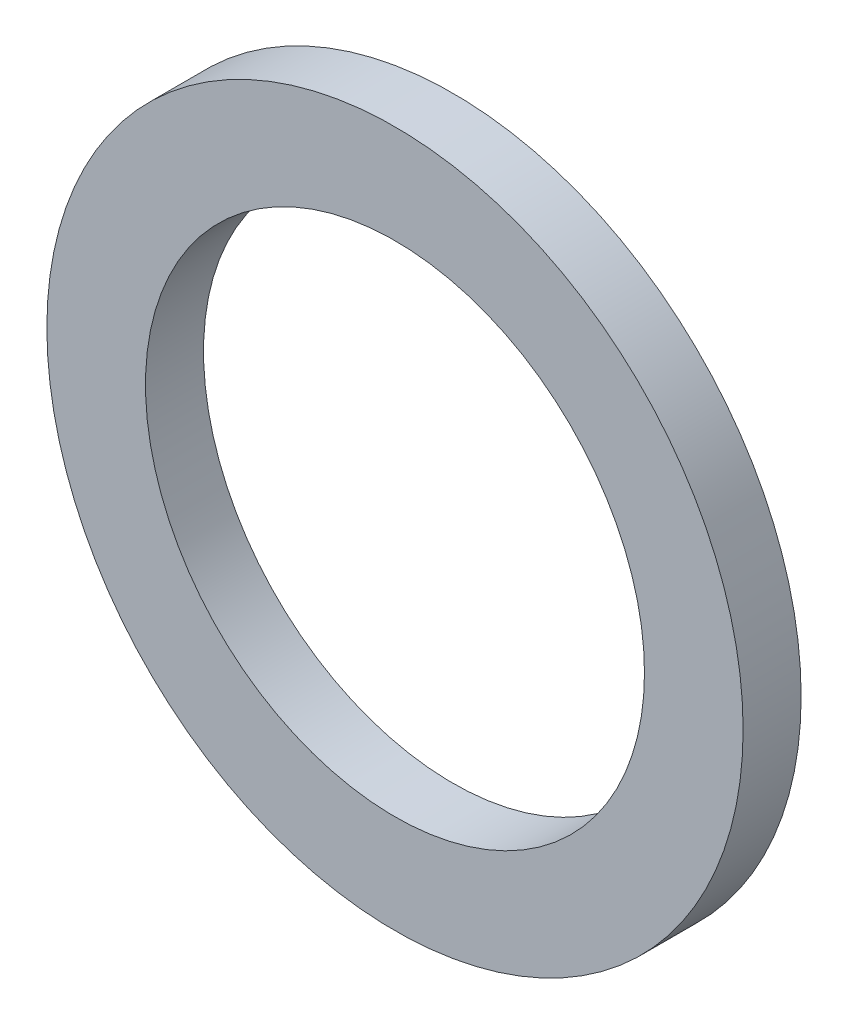
SolidWorks part; units mm, degrees
ref_plane "Front Plane" through (0, 0, 0) normal (0, 0, 1) x (1, 0, 0)
ref_plane "Top Plane" through (0, 0, 0) normal (0, 1, 0) x (1, 0, 0)
ref_plane "Right Plane" through (0, 0, 0) normal (1, 0, 0) x (0, 0, -1)
sketch "Sketch1" plane through (0, 0, 0) normal (0, 0, 1) x (1, 0, 0)
  circle A0 centre (0, 0) radius 2.15
  circle A1 centre (0, 0) radius 3
  dimension "D1" = 4.3
  dimension "D2" = 6
extrude "Boss-Extrude1" add sketch "Sketch1" along normal blind 0.5
